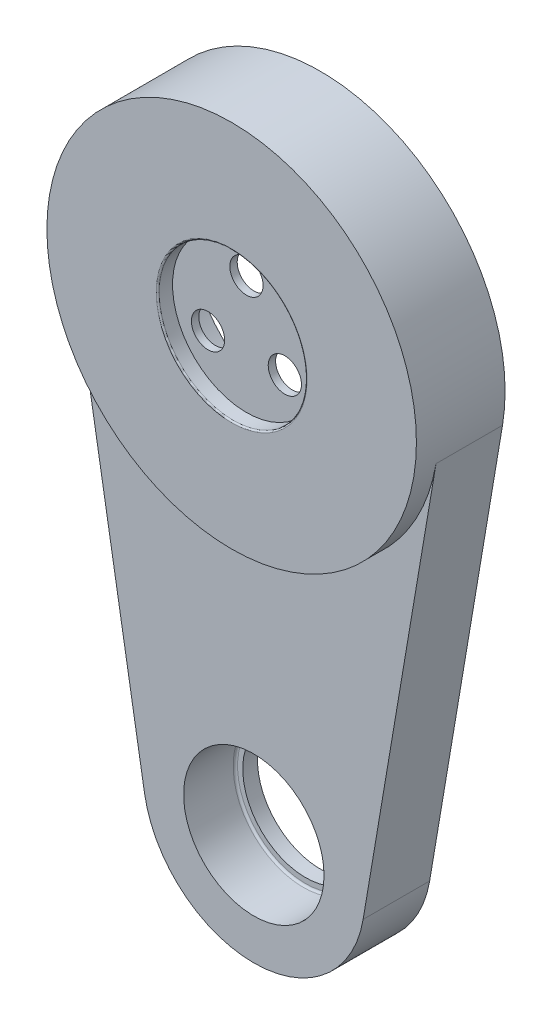
SolidWorks part; units mm, degrees
other "마크업1"
sketch "스케치14" plane through (30, 31, -30.5354) normal (0.2605, 0.9636, -0.0594) x (0.9655, -0.2601, 0.014)
sketch "스케치15" plane through (30, 31, -30.5354) normal (0.2605, 0.9636, -0.0594) x (0.9655, -0.2601, 0.014)
sketch "스케치16" plane through (30, 31, -30.5354) normal (0.2605, 0.9636, -0.0594) x (0.9655, -0.2601, 0.014)
sketch "스케치21" plane through (30, 31, -30.5354) normal (0.2605, 0.9636, -0.0594) x (0.9655, -0.2601, 0.014)
sketch "스케치23" plane through (30, 275, -27) normal (0.2605, 0.9636, -0.0594) x (0.9655, -0.2601, 0.014)
sketch "스케치28" plane through (20, 265, -24) normal (0.2605, 0.9636, -0.0594) x (0.9655, -0.2601, 0.014)
sketch "스케치31" plane through (20, 265, -24) normal (0.2605, 0.9636, -0.0594) x (0.9655, -0.2601, 0.014)
sketch "스케치32" plane through (20, 265, -23) normal (0.2605, 0.9636, -0.0594) x (0.9655, -0.2601, 0.014)
sketch "스케치33" plane through (20, 265, -23) normal (0.2605, 0.9636, -0.0594) x (0.9655, -0.2601, 0.014)
sketch "스케치52" plane through (24, 65, -12) normal (0.2605, 0.9636, -0.0594) x (0.9655, -0.2601, 0.014)
sketch "스케치61" plane through (22.5, 22.5, -13) normal (0.2605, 0.9636, -0.0594) x (0.9655, -0.2601, 0.014)
sketch "스케치64" plane through (22.5, 22.5, -13) normal (0.2605, 0.9636, -0.0594) x (0.9655, -0.2601, 0.014)
sketch "스케치70" plane through (22.5, 22.5, -13) normal (0.2605, 0.9636, -0.0594) x (0.9655, -0.2601, 0.014)
sketch "스케치71" plane through (22.5, 22.5, -13) normal (0.2605, 0.9636, -0.0594) x (0.9655, -0.2601, 0.014)
sketch "스케치72" plane through (22.5, 22.5, -13) normal (0.2605, 0.9636, -0.0594) x (0.9655, -0.2601, 0.014)
sketch "스케치77" plane through (22.5, 22.5, -13) normal (0.2605, 0.9636, -0.0594) x (0.9655, -0.2601, 0.014)
sketch "스케치78" plane through (22.5, 22.5, -13) normal (0.2605, 0.9636, -0.0594) x (0.9655, -0.2601, 0.014)
sketch "스케치79" plane through (25, 25, -13) normal (0.2605, 0.9636, -0.0594) x (0.9655, -0.2601, 0.014)
sketch "스케치80" plane through (25, 25, -13) normal (0.2605, 0.9636, -0.0594) x (0.9655, -0.2601, 0.014)
sketch "스케치81" plane through (25, 25, -13) normal (0.2605, 0.9636, -0.0594) x (0.9655, -0.2601, 0.014)
sketch "스케치82" plane through (25, 25, -13) normal (0.2605, 0.9636, -0.0594) x (0.9655, -0.2601, 0.014)
sketch "스케치83" plane through (25, 25, -12) normal (0.2605, 0.9636, -0.0594) x (0.9655, -0.2601, 0.014)
sketch "스케치84" plane through (25, 25, -12) normal (0.2605, 0.9636, -0.0594) x (0.9655, -0.2601, 0.014)
sketch "스케치85" plane through (25, 25, -12) normal (0.2605, 0.9636, -0.0594) x (0.9655, -0.2601, 0.014)
material "7075-T6 (SN)"
ref_plane "정면" through (0, 0, 0) normal (0, 0, 1) x (1, 0, 0)
ref_plane "윗면" through (0, 0, 0) normal (0, 1, 0) x (1, 0, 0)
ref_plane "우측면" through (0, 0, 0) normal (1, 0, 0) x (0, 0, -1)
sketch "스케치2" plane through (0, 6, 0) normal (0, 0, -1) x (1, 0, 0)
  circle A0 centre (0, 6) radius 25
  dimension "D1" = 50
extrude "보스-돌출2" add sketch "스케치2" along normal blind 2
sketch "스케치22" plane through (0, 0, 0) normal (0, 0, 1) x (1, 0, 0)
  circle A0 centre (0, 0) radius 10
  dimension "D1" = 20
extrude "컷-돌출1" cut sketch "스케치22" against normal blind 2 contours A0
fillet "필렛4" radius 0.2 1 edges at (10, 0, 0)
sketch "스케치54" plane through (0, 0, -2) normal (0, 0, -1) x (-1, 0, 0)
  circle A4 centre (0, 0) radius 25 construction
  circle A5 centre (0, 0) radius 25
extrude "보스-돌출6" add sketch "스케치54" along normal blind 10
sketch "스케치55" plane through (0, 0, -12) normal (0, 0, -1) x (-1, 0, 0)
  circle A0 centre (0, 0) radius 18.5
  dimension "D1" = 37
extrude "컷-돌출2" cut sketch "스케치55" against normal blind 8
sketch "스케치56" plane through (0, 0, -4) normal (0, 0, -1) x (-1, 0, 0)
  circle A0 centre (0, 0) radius 6 construction
  point P3 (0, 6)
  dimension "D1" = 12
hole_wizard "M4 육각 소켓 머리 캡 나사용 카운터보어1" positions "스케치57" profile "스케치58" counterbore size "M4" standard "ISO" end condition through all
sketch "스케치57" plane through (0, 0, -4) normal (0, 0, -1) x (-1, 0, 0)
  point P0 (0, 6)
sketch "스케치58" plane through (0, 6, -4) normal (1, 0, 0) x (0, 1, 0)
  line L0 (0, 0) -> (0, 4)
  line L1 (0, 4) -> (2.25, 4)
  line L3 (2.25, 4) -> (2.25, 1)
  line L4 (2.25, 1) -> (4, 1)
  line L5 (4, 1) -> (4, 0)
  line L7 (4, 0) -> (0, 0)
  line L11 (0, -6.35) -> (0, 107.95) construction
  dimension "관통 구멍 지름" = 4.5
  dimension "관통 구멍 깊이" = 4
  dimension "카운터보어 지름" = 8
  dimension "카운터보어 깊이" = 1
pattern_circular "원형 패턴1" count 3 over 360 about axis through (0, 0, 0) along (0, 0, 1) of "M4 육각 소켓 머리 캡 나사용 카운터보어1"
sketch "스케치59" plane through (0, 0, -4) normal (0, 0, -1) x (-1, 0, 0)
  circle A0 centre (0, 0) radius 17.5
  circle A1 centre (0, 0) radius 18.5 construction
  circle A2 centre (0, 0) radius 18.5
  dimension "D1" = 35
extrude "보스-돌출7" add sketch "스케치59" along normal blind 1
sketch "스케치60" plane through (0, 0, -12) normal (0, 0, -1) x (-1, 0, 0)
  line L0 (-24.6503, -4.1667) -> (-14.7902, -62.5)
  line L1 (0, 0) -> (0, -60) construction
  line L2 (24.6503, -4.1667) -> (14.7902, -62.5)
  circle A0 centre (0, 0) radius 25 construction
  arc A1 (-14.7902, -62.5) -> (14.7902, -62.5) centre (0, -60) ccw
  arc A2 (-24.6503, -4.1667) -> (24.6503, -4.1667) centre (0, 0) ccw
  dimension "D2" = 30
  dimension "D1" = 60
extrude "보스-돌출8" add sketch "스케치60" against normal blind 9
fillet "필렛6" radius 0.3 1 edges at (-18.5, 0, -5)
sketch "스케치68" plane through (0, 0, -3) normal (0, 0, 1) x (1, 0, 0)
  circle A0 centre (0, -60) radius 9.5
  dimension "D1" = 19
extrude "컷-돌출7" cut sketch "스케치68" against normal blind 7
sketch "스케치69" plane through (0, 0, -10) normal (0, 0, 1) x (1, 0, 0)
  circle A0 centre (0, -60) radius 8.5
  dimension "D1" = 17
extrude "컷-돌출8" cut sketch "스케치69" against normal through all
fillet "필렛7" radius 0.3 1 edges at (9.5, -60, -10)
